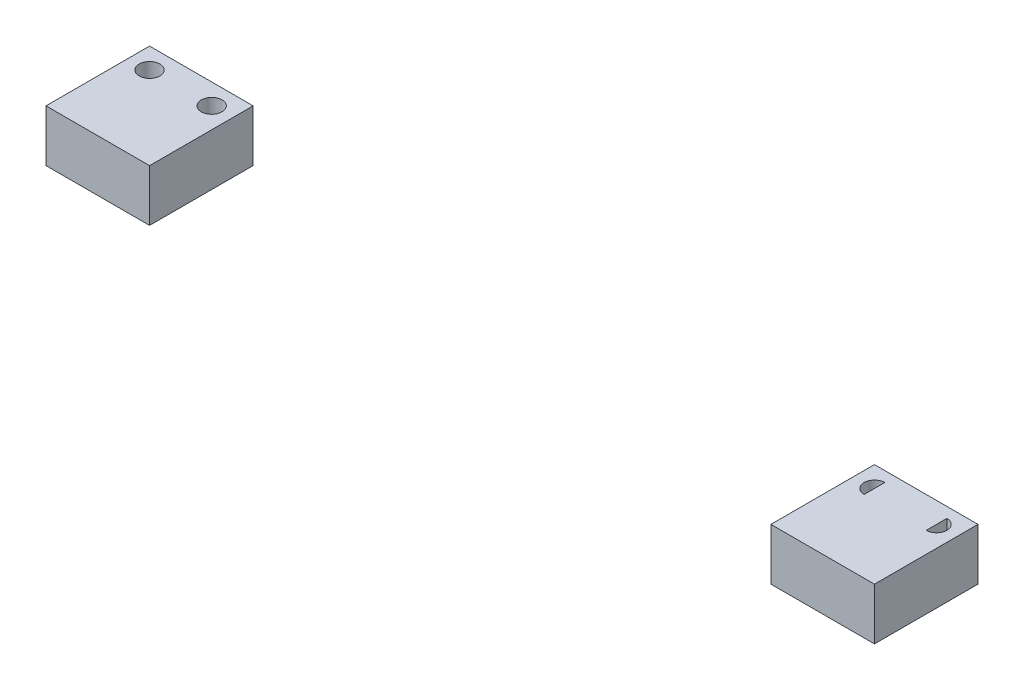
SolidWorks part; units mm, degrees
ref_plane "Front Plane" through (0, 0, 0) normal (0, 0, 1) x (1, 0, 0)
ref_plane "Top Plane" through (0, 0, 0) normal (0, 1, 0) x (1, 0, 0)
ref_plane "Right Plane" through (0, 0, 0) normal (1, 0, 0) x (0, 0, -1)
sketch "Sketch1" plane through (0, 0, 0) normal (0, 1, 0) x (1, 0, 0)
  line L1 (-40, 5) -> (-30, 5)
  line L2 (-40, 5) -> (-40, -5)
  line L3 (-40, -5) -> (-30, -5)
  line L4 (-30, 5) -> (-30, -5)
  line L5 (-40, 5) -> (-30, -5) construction
  line L6 (-40, -5) -> (-30, 5) construction
  point P0 (-35, 0)
  dimension "D1" = 10
  dimension "D2" = 10
  dimension "D3" = 30
  dimension "D4" = 5
extrude "Boss-Extrude1" add sketch "Sketch1" along normal mid plane 5
mirror "Mirror1" about plane through (0, 0, 0) normal (1, 0, 0) of bodies 101
sketch "Sketch3" plane through (0, 2.5, 0) normal (0, 1, 0) x (1, 0, 0)
  line L0 (-30, 5) -> (-40, 5) construction
  line L2 (-40, 5) -> (-40, -5) construction
  circle A0 centre (-38, 3) radius 1
  point P6 (-40, 3.7943)
  point P7 (-34.8668, 6.5189)
  dimension "D1" = 2
  dimension "D2" = 2
  dimension "D3" = 2
extrude "Cut-Extrude2" cut sketch "Sketch3" against normal through all
ref_plane "Plane1" through (-35, 0, 0) normal (-1, 0, 0) x (0, 0, 1)
mirror "Mirror3" about plane through (-35, 0, 0) normal (-1, 0, 0) of "Cut-Extrude2"
sketch "Sketch4" plane through (0, 2.5, 0) normal (0, 1, 0) x (1, 0, 0)
  line L0 (32, 4) -> (32, 2)
  line L1 (30, -5) -> (30, 5) construction
  line L2 (30, 5) -> (40, 5) construction
  arc A0 (32, 2) -> (32, 4) centre (32, 3) cw
  dimension "D2" = 1
  dimension "D1" = 2
  dimension "D3" = 2
  dimension "D4" = 2
extrude "Cut-Extrude3" cut sketch "Sketch4" against normal through all
ref_plane "Plane2" through (35, 0, 0) normal (-1, 0, 0) x (0, 0, 1)
mirror "Mirror4" about plane through (35, 0, 0) normal (-1, 0, 0) of "Cut-Extrude3"
